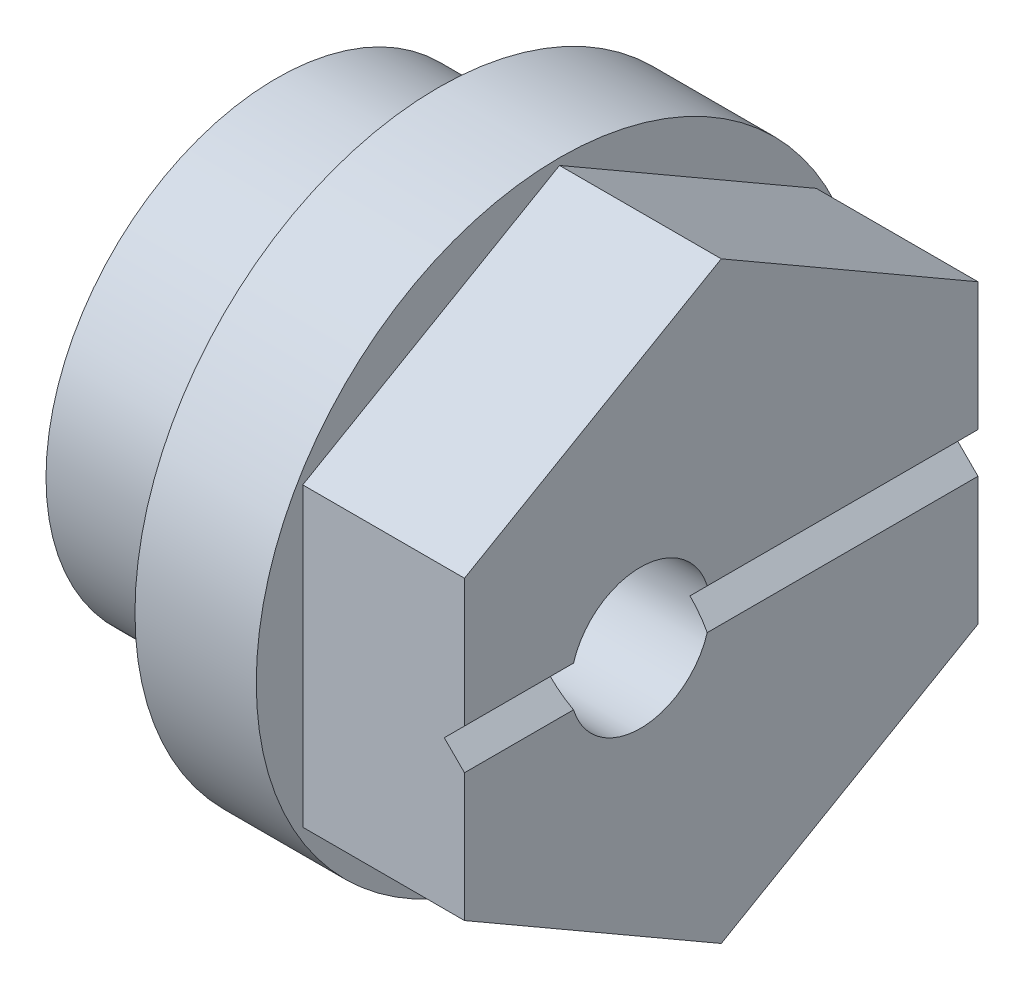
SolidWorks part; units mm, degrees
material "Phosphor bronze 10% D, UNS C52400"
ref_plane "Front Plane" through (0, 0, 0) normal (0, 0, 1) x (1, 0, 0)
ref_plane "Top Plane" through (0, 0, 0) normal (0, 1, 0) x (1, 0, 0)
ref_plane "Right Plane" through (0, 0, 0) normal (1, 0, 0) x (0, 0, -1)
sketch "Sketch1" plane through (0, 0, 0) normal (0, 0, 1) x (1, 0, 0)
  line L0 (4, 7.5) -> (4, 0)
  line L1 (4, 0) -> (7, 0)
  line L2 (7, 0) -> (7, 7.5)
  line L3 (7, 7.5) -> (4, 7.5)
  line L4 (4, 0) -> (7, 0) construction
  dimension "D1" = 3
  dimension "D2" = 7.5
revolve "Revolve1" add sketch "Sketch1" angle 360 about L4
sketch "Sketch2" plane through (7, 0, 0) normal (1, 0, 0) x (0, 0, -1)
  line L0 (0, -7.3323) -> (-6.35, -3.6662)
  line L1 (-6.35, -3.6662) -> (-6.35, 3.6662)
  line L2 (-6.35, 3.6662) -> (0, 7.3323)
  line L3 (0, 7.3323) -> (6.35, 3.6662)
  line L4 (6.35, 3.6662) -> (6.35, -3.6662)
  line L5 (6.35, -3.6662) -> (0, -7.3323)
  circle A0 centre (0, 0) radius 7.5 construction
  dimension "D1" = 6.35
  dimension "D2" = 6.35
  dimension "D3" = 3.6662
  dimension "D4" = 7.3323
  dimension "D5" = 3.6662
  dimension "D6" = 7.3323
extrude "Boss-Extrude1" add sketch "Sketch2" along normal blind 4
sketch "Sketch3" plane through (0, 0, 6.35) normal (0, 0, 1) x (1, 0, 0)
  line L0 (11, -0.5) -> (11, 0.5)
  line L1 (11, 0.5) -> (10.5, 0)
  line L2 (10.5, 0) -> (11, -0.5)
  line L3 (7, 3.6662) -> (7, -3.6662) construction
  line L4 (11, -3.6662) -> (7, -3.6662) construction
  dimension "D1" = 3.5
  dimension "D2" = 4
  dimension "D3" = 3.1662
  dimension "D4" = 3.6662
  dimension "D5" = 4.1662
extrude "Cut-Extrude1" cut sketch "Sketch3" against normal through all
sketch "Sketch4" plane through (4, 0, 0) normal (-1, 0, 0) x (0, 0, 1)
  circle A0 centre (0, 0) radius 5.7
  circle A1 centre (0, 0) radius 7.5 construction
  dimension "D1" = 11.4
extrude "Boss-Extrude2" add sketch "Sketch4" along normal blind 4
hole_wizard "CBORE for #5 Button Head Cap Screw1" positions "Sketch6" profile "Sketch5" counterbore size "#5" standard "ANSI Inch" end condition through all
sketch "Sketch6" plane through (0, 0, 0) normal (-1, 0, 0) x (0, 0, 1)
  point P0 (2, 0)
sketch "Sketch5" plane through (0, 0, 2) normal (0, 1, 0) x (0, 0, 1)
  line L0 (0, 0) -> (0, 11)
  line L1 (0, 11) -> (0.7937, 11)
  line L3 (0.7937, 11) -> (0.7937, 7.9375)
  line L4 (0.7937, 7.9375) -> (3.3, 7.9375)
  line L5 (3.3, 7.9375) -> (3.3, 0)
  line L7 (3.3, 0) -> (0, 0)
  line L11 (0, -6.35) -> (0, 107.95) construction
  dimension "Thru Hole Dia." = 1.5875
  dimension "Thru Hole Depth" = 11
  dimension "C'Bore Dia." = 6.6
  dimension "C'Bore Depth" = 7.9375
hole_wizard "#8-32 Tapped Hole1" positions "Sketch8" profile "Sketch7" tap size "#8-32" standard "Ansi Inch" end condition through all
sketch "Sketch8" plane through (11, 0, 0) normal (1, 0, 0) x (0, 0, -1)
  arc A0 (-1.3835, 0.5) -> (-2.6165, 0.5) centre (-2, 0) ccw construction
  point P0 (-2, 0)
sketch "Sketch7" plane through (11, 0, 2) normal (0, 1, 0) x (0, 0, -1)
  line L0 (0, 0) -> (0, 11)
  line L1 (0, 11) -> (1.7272, 11)
  line L2 (1.7272, 11) -> (1.7272, 0)
  line L5 (1.7272, 0) -> (0, 0)
  line L11 (0, -6.35) -> (0, 107.95) construction
  dimension "Thru Tap Drill Dia." = 3.4544
  dimension "Thru Tap Drill Depth" = 11
cosmetic thread "Hole Thread1" parameters "D1"=6, "D2"=4.1656
